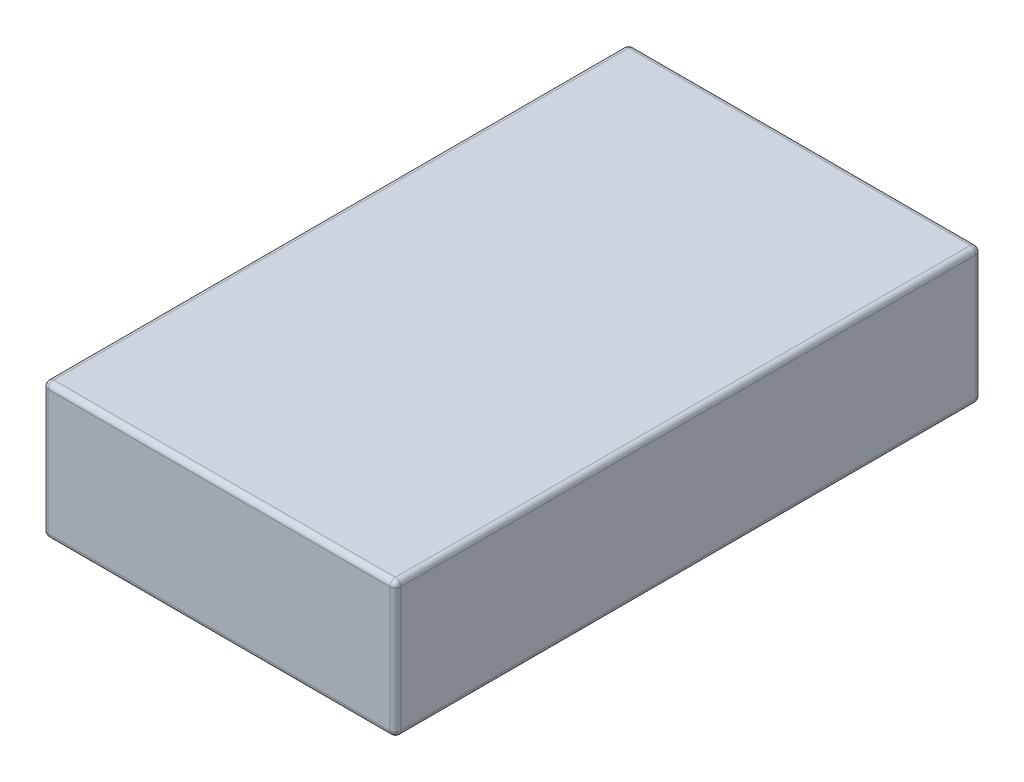
SolidWorks part; units mm, degrees
ref_plane "Front" through (0, 0, 0) normal (0, 0, 1) x (1, 0, 0)
ref_plane "Top" through (0, 0, 0) normal (0, 1, 0) x (1, 0, 0)
ref_plane "Right" through (0, 0, 0) normal (1, 0, 0) x (0, 0, -1)
sketch "Sketch1" plane through (0, 0, 0) normal (0, 1, 0) x (1, 0, 0)
  line L1 (-32.5, -54) -> (32.5, -54)
  line L2 (-32.5, -54) -> (-32.5, 54)
  line L3 (-32.5, 54) -> (32.5, 54)
  line L4 (32.5, -54) -> (32.5, 54)
  line L5 (-32.5, -54) -> (32.5, 54) construction
  line L6 (-32.5, 54) -> (32.5, -54) construction
  point P0 (0, 0)
  dimension "D1" = 65
  dimension "D2" = 108
extrude "Boss-Extrude1" add sketch "Sketch1" along normal blind 25
fillet "Fillet1" radius 1 12 edges at (-32.5, 0, 0) (0, 0, -54) (32.5, 12.5, -54) (-32.5, 12.5, 54) (32.5, 25, 0) (0, 25, 54) (-32.5, 12.5, -54) (32.5, 12.5, 54) (-32.5, 25, 0) (0, 25, -54) (0, 0, 54) (32.5, 0, 0)
